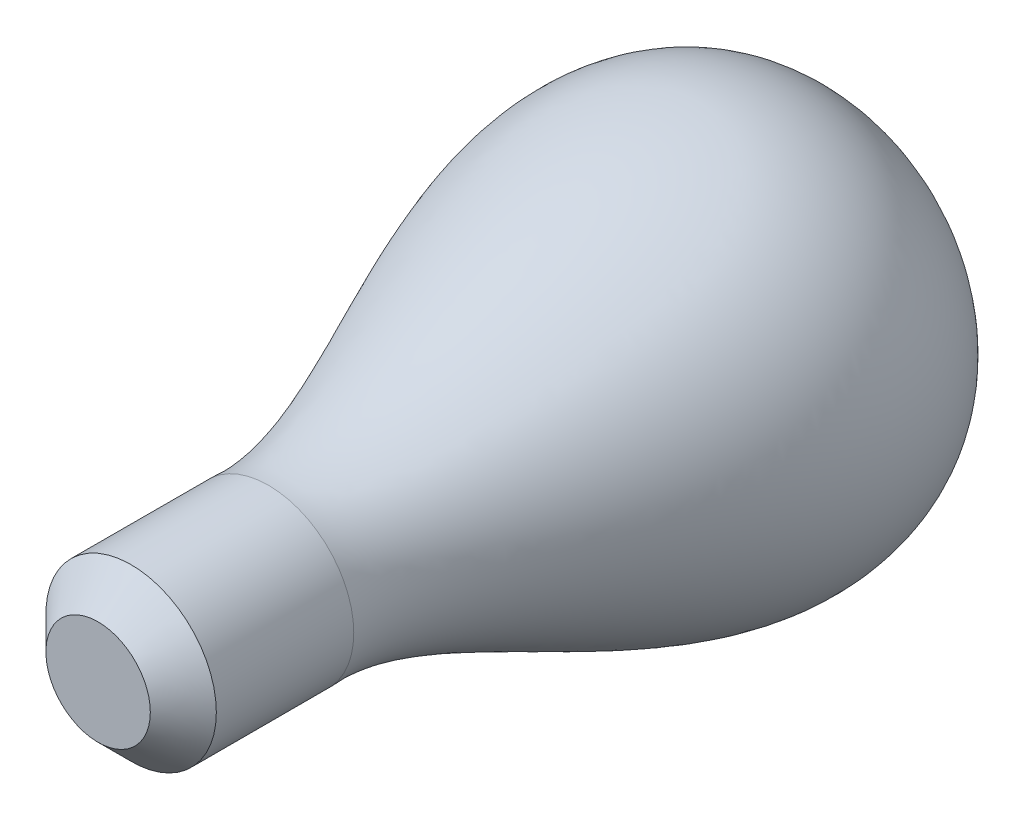
SolidWorks part; units mm, degrees
ref_plane "Front Plane" through (0, 0, 0) normal (0, 0, 1) x (1, 0, 0)
ref_plane "Top Plane" through (0, 0, 0) normal (0, 1, 0) x (1, 0, 0)
ref_plane "Right Plane" through (0, 0, 0) normal (1, 0, 0) x (0, 0, -1)
sketch "Sketch1" plane through (0, 0, 0) normal (0, 0, 1) x (1, 0, 0)
  circle A0 centre (0, 0) radius 12.7
  dimension "D1" = 25.4
extrude "Boss-Extrude1" add sketch "Sketch1" along normal blind 25.4
sketch "Sketch2" plane through (0, 0, 0) normal (0, 1, 0) x (1, 0, 0)
  line L0 (0, 0) -> (0, 91.44)
  line L1 (0, 0) -> (-12.7, 0)
  spline S0 degree 3 poles (0, 91.44) (-22.3133, 89.8695) (-44.0305, 54.7768) (-11.1289, 19.0358) (-12.7, 0) knots 0 0 0 0 0.356051 1 1 1 1
  dimension "D1" = 91.44
  dimension "D2" = 30.1625
revolve "Revolve1" add sketch "Sketch2" angle 360 about L0
chamfer "Chamfer1" distance 4.92 angle 45 1 edges at (12.7, 0, 25.4)
sketch "Sketch3" plane through (0, 0, 0) normal (0, 1, 0) x (1, 0, 0)
  line L0 (0, -25.4) -> (0, 91.44) construction
  line L1 (-7.78, -25.4) -> (7.78, -25.4) construction
  dimension "D1" = 116.84
